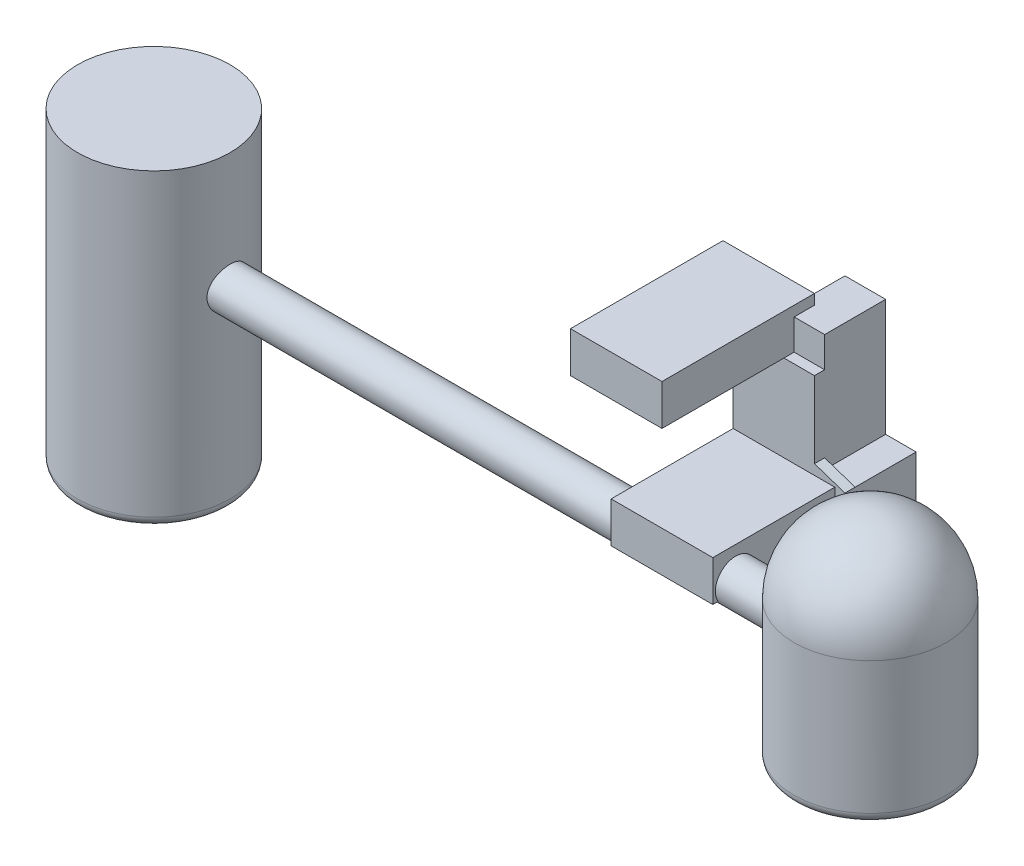
SolidWorks part; units mm, degrees
ref_plane "Front Plane" through (0, 0, 0) normal (0, 0, 1) x (1, 0, 0)
ref_plane "Top Plane" through (0, 0, 0) normal (0, 1, 0) x (1, 0, 0)
ref_plane "Right Plane" through (0, 0, 0) normal (1, 0, 0) x (0, 0, -1)
sketch "Sketch1" plane through (0, 0, 0) normal (0, 1, 0) x (1, 0, 0)
  line L1 (-4500, -7500) -> (4500, -7500)
  line L2 (-4500, -7500) -> (-4500, 7500)
  line L3 (-4500, 7500) -> (4500, 7500)
  line L4 (4500, -7500) -> (4500, 7500)
  line L5 (-4500, -7500) -> (4500, 7500) construction
  line L6 (-4500, 7500) -> (4500, -7500) construction
  point P0 (0, 0)
  dimension "D1" = 15000
  dimension "D2" = 9000
extrude "Boss-Extrude1" add sketch "Sketch1" along normal blind 4000
sketch "Sketch2" plane through (0, 0, -7500) normal (0, 0, -1) x (-1, 0, 0)
  line L1 (-4500, 0) -> (-3500, 0)
  line L2 (-4500, 0) -> (-4500, 3000)
  line L3 (-4500, 3000) -> (-3500, 3000)
  line L4 (-3500, 0) -> (-3500, 3000)
  line L5 (-4500, 3000) -> (-7500, 3000)
  line L6 (-4500, 3000) -> (-4500, 0)
  line L7 (-4500, 0) -> (-7500, 0)
  line L8 (-7500, 3000) -> (-7500, 0)
  point P7 (-7313.5259, 2716.2732)
  line M1 (-4500, 0) -> (4500, 0)
  line M4 (-4500, 4000) -> (-4500, 0)
  dimension "D1" = 4000
  dimension "D2" = 1000
  dimension "3m" = 3000
extrude "Boss-Extrude2" add sketch "Sketch2" along normal blind 4000 and the other way blind 2000 contours L5 L8 L7 M4 | L4 L3 M1 M4
sketch "Sketch3" plane through (0, 0, 0) normal (0, -1, 0) x (1, 0, 0)
  line L0 (3500, -11500) -> (7500, -11500) construction
  line L1 (10500, -11500) -> (-500, -11500)
  line L2 (10500, -11500) -> (10500, -4500)
  line L3 (10500, -4500) -> (-500, -4500)
  line L4 (-500, -11500) -> (-500, -4500)
  point P5 (3500, -11500)
  point P12 (7500, -11500)
  dimension "D1" = 11000
  dimension "D2" = 4000
  dimension "D3" = 7000
extrude "Boss-Extrude3" add sketch "Sketch3" along normal blind 12500
sketch "Sketch4" plane through (0, -12500, 0) normal (0, -1, 0) x (1, 0, 0)
  line L1 (10500, -11500) -> (3500, -11500)
  line L2 (10500, -11500) -> (10500, -7500)
  line L3 (10500, -7500) -> (3500, -7500)
  line L4 (3500, -11500) -> (3500, -7500)
  dimension "D1" = 7000
  dimension "D2" = 4000
extrude "Boss-Extrude4" add sketch "Sketch4" along normal blind 1500
sketch "Sketch5" plane through (0, 0, -4500) normal (0, 0, 1) x (1, 0, 0)
  line L1 (-500, -12500) -> (9500, -12500)
  line L2 (-500, -12500) -> (-500, -8500)
  line L3 (-500, -8500) -> (9500, -8500)
  line L4 (9500, -12500) -> (9500, -8500)
  dimension "D1" = 10000
  dimension "D2" = 4000
extrude "Boss-Extrude5" add sketch "Sketch5" along normal blind 12000
sketch "Sketch6" plane through (9500, 0, 0) normal (1, 0, 0) x (0, 0, -1)
  line L0 (-7250, -11500) -> (-7500, -11500) construction
  line L1 (-7500, -12500) -> (-7500, -8500) construction
  line L2 (-7500, -12500) -> (4500, -12500) construction
  circle A0 centre (-5250, -11500) radius 2000
  point P2 (-7151.0037, -9125.4182)
  point P9 (0, 0)
  point P10 (0, 0)
  point P11 (-6775.0954, -9500)
  dimension "D1" = 4000
  dimension "D2" = 1000
  dimension "D3" = 250
extrude "Boss-Extrude6" add sketch "Sketch6" along normal blind 6000
ref_plane "Plane1" through (0, -10500, 0) normal (0, -1, 0) x (-1, 0, 0)
sketch "Sketch9" plane through (0, -10500, 0) normal (0, -1, 0) x (-1, 0, 0)
  circle A0 centre (-22728.4161, -5250) radius 7500
  point P2 (-15500, -3250)
  point P3 (-15500, -7250)
  point P5 (0, 0)
  point P7 (0, 0)
  dimension "D1" = 15000
extrude "Boss-Extrude8" add sketch "Sketch9" against normal blind 4000 and the other way blind 10000
sketch "Sketch10" plane through (0, -6500, 0) normal (0, 1, 0) x (1, 0, 0)
  line L0 (15228.4161, -5250) -> (30228.4161, -5250)
  arc A0 (15500, -3250) -> (15500, -7250) centre (22728.4161, -5250) ccw construction
  circle A1 centre (22728.4161, -5250) radius 7500 construction
  arc A2 (15228.4161, -5250) -> (30228.4161, -5250) centre (22728.4161, -5250) cw
revolve "Revolve5" add sketch "Sketch10" angle 180 about L0
sketch "Sketch12" plane through (-500, 0, 0) normal (-1, 0, 0) x (0, 0, 1)
  arc A0 (3517.9492, -12500) -> (6982.0508, -12500) centre (5250, -11500) ccw construction
  arc A1 (6982.0508, -12500) -> (3517.9492, -12500) centre (5250, -11500) ccw construction
  arc A2 (3517.9492, -12500) -> (6982.0508, -12500) centre (5250, -11500) ccw
  arc A3 (6982.0508, -12500) -> (3517.9492, -12500) centre (5250, -11500) ccw
extrude "Boss-Extrude9" add sketch "Sketch12" along normal blind 40000
sketch "Sketch16" plane through (0, -10500, 0) normal (0, -1, 0) x (-1, 0, 0)
  circle A0 centre (47728.4161, -5250) radius 7500
  point P2 (40500, -3250)
  point P3 (40500, -7250)
  point P5 (0, 0)
  point P7 (0, 0)
  dimension "15m" = 15000
extrude "Boss-Extrude11" add sketch "Sketch16" against normal up to surface (10500 mm away) and the other way blind 20000 up to face at (-166.6667, 0, -1500)
sketch "Sketch18" plane through (-500, 0, 0) normal (1, 0, 0) x (0, 0, -1)
  line L1 (-3517.9492, -12500) -> (-6982.0508, -12500)
  line L2 (-3517.9492, -12500) -> (-6982.0508, -12500)
  arc A1 (-6982.0508, -12500) -> (-3517.9492, -12500) centre (-5250, -11500) ccw
  arc A2 (-6982.0508, -12500) -> (-3517.9492, -12500) centre (-5250, -11500) ccw
  dimension "D1" = 0
extrude "Boss-Extrude12" add sketch "Sketch18" along normal up to surface (10000 mm away) up to face at (9500, -13000, 5250)
fillet "Fillet1" radius 1000 1 edges at (22728.4161, -20500, -2250)
fillet "Fillet2" radius 1000 1 edges at (-47728.4161, -30500, -2250)
sketch "Sketch19" plane through (0, 0, 0) normal (0, 1, 0) x (1, 0, 0)
  line L1 (10500, 11500) -> (7500, 11500)
  line L2 (10500, 11500) -> (10500, 5500)
  line L3 (10500, 5500) -> (7500, 5500)
  line L4 (7500, 11500) -> (7500, 5500)
extrude "Cut-Extrude1" cut sketch "Sketch19" against normal up to surface (8500 mm away) up to face at (4500, -8500, 1500)
sketch "Sketch20" plane through (0, 0, -5500) normal (0, 0, -1) x (-1, 0, 0)
  line L0 (-10500, -8500) -> (-7500, -7500)
  line L1 (-7500, 3000) -> (-7500, -8500) construction
  line L2 (-7500, -8500) -> (-10500, -8500) construction
  line L3 (-7500, -8500) -> (-10500, -8500)
  line L4 (-7500, -7500) -> (-7500, -8500)
  line L9 (-7500, -8500) -> (-7500, 0)
  line L10 (-7500, 0) -> (-10500, 0)
  line L11 (-10500, 0) -> (-10500, -8500)
  line L12 (-10500, -8500) -> (-7500, -8500)
  line L13 (-7500, -8500) -> (-7500, 0)
  line L14 (-7500, 0) -> (-10500, 0)
  line L15 (-10500, 0) -> (-10500, -8500)
  line L16 (-10500, -8500) -> (-7500, -8500)
  line M5 (-7500, -8500) -> (-7500, 0)
  line M6 (-7500, 0) -> (-10500, 0)
  line M7 (-10500, 0) -> (-10500, -8500)
  dimension "D1" = 1000
  dimension "D2" = 0
extrude "Cut-Extrude2" cut sketch "Sketch20" against normal through all both and the other way through all contours L0 M7 M5 M6
ref_plane "Plane3" through (0, 0, 0) normal (0, -1, 0) x (-1, 0, 0)
sketch "Sketch22" plane through (0, 0, -5500) normal (0, 0, 1) x (1, 0, 0)
  line L0 (-4500, 0) -> (4500, 0) construction
  line L1 (-4500, 0) -> (4500, 0)
  line L2 (4500, 0) -> (7500, 0)
